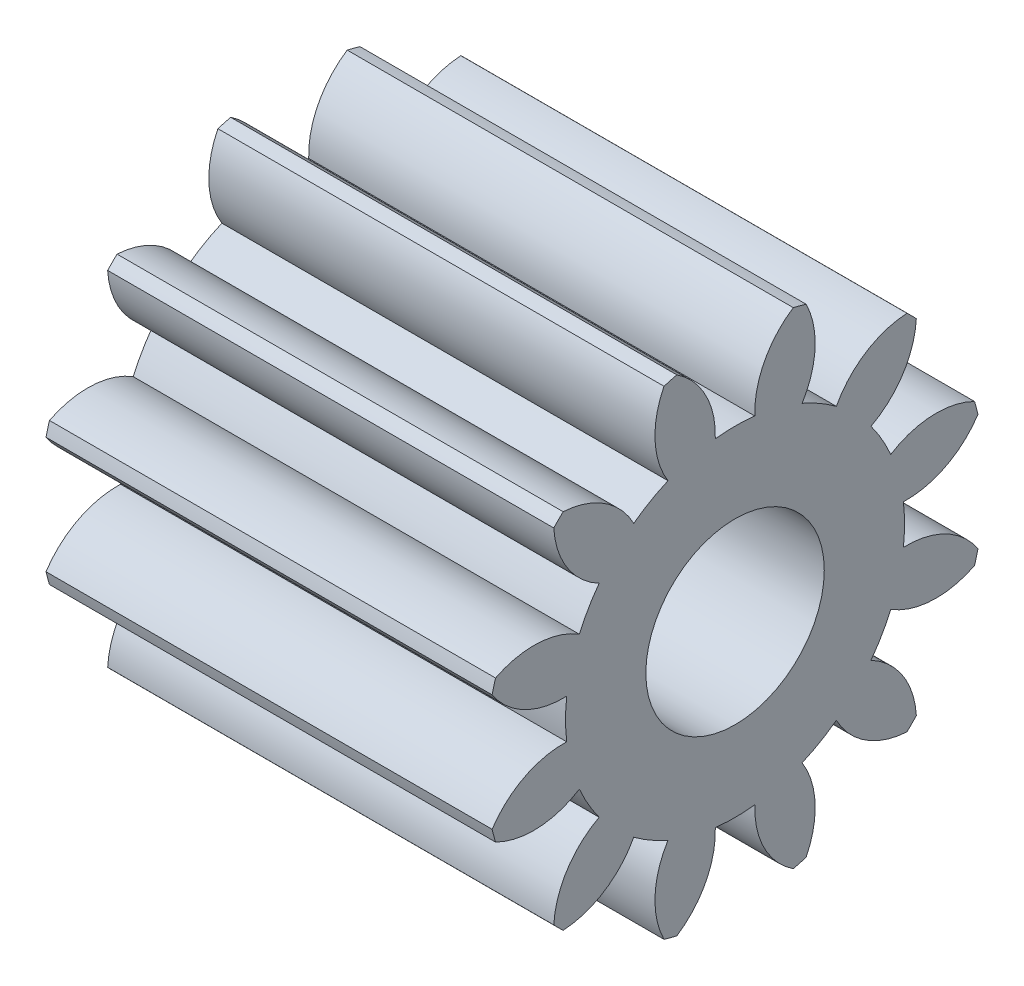
SolidWorks part; units mm, degrees
ref_plane "Plane1" through (0, 0, 0) normal (0, 0, 1) x (1, 0, 0)
ref_plane "Plane2" through (0, 0, 0) normal (0, 1, 0) x (1, 0, 0)
ref_plane "Plane3" through (0, 0, 0) normal (1, 0, 0) x (0, 0, -1)
sketch "HoldingSke" [suppressed] plane through (0, 0, 0) normal (0, 1, 0) x (1, 0, 0)
  line L0 (0, 0) -> (0.1223, -0.026)
  line L1 (-15, 0) -> (100, 0) construction
  line L2 (0, 0) -> (-2.1039, 2.3779)
  line L3 (0, 0) -> (-11.863, 4.5341)
  line L4 (0, 0) -> (8.4473, 1.7955)
  line L5 (0, 0) -> (-46.8476, -17.4728)
  line L6 (0, 0) -> (-82.8963, -55.9304)
  line L7 (-2.1039, 2.3779) -> (19.4211, 100.0338)
  line L8 (-76.2, 54.61) -> (-72.9, 54.61)
  line L9 (-71.009, 38.7566) -> (-53.1078, 45.2721)
  line L10 (-76.2, 71.12) -> (104.1128, 71.12)
  line L11 (0, 0) -> (-100, 0)
  line L12 (-76.2, 101.6) -> (-75.945, 101.6)
  line L13 (24.9733, 27.94) -> (52.9518, 28.4284)
  line L14 (24.9733, 27.94) -> (24.9743, 27.94)
  line L15 (24.9733, 27.94) -> (100.4006, 29.5858)
  line L16 (-63.627, -8) -> (-12.827, -8)
  circle A0 centre (0, 0) radius 20
  circle A1 centre (0, 0) radius 37.5
  circle A2 centre (0, 0) radius 37.5
  circle A3 centre (0, 0) radius 20
  dimension "MHD" = 75
  dimension "Hub_dia" = 75
  dimension "Bore" = 40
  dimension "MBD" = 40
  dimension "Num_teeth" = 12
  dimension "Pitch" = 0.125
  dimension "Overall_len" = 50
  dimension "Show_teeth" = 12
  dimension "Thickness" = 100
  dimension "OAL" = 100.0001
  dimension "T_dim" = 3.3
  dimension "Ap" = 20
  dimension "H" = 19.05
  dimension "Pitch_radius" = 180.3128
  dimension "Width" = 100
  dimension "Backlash" = 0.255
  dimension "Addendum_fac" = 1
  dimension "Dedendum_fac" = 1.25
  dimension "Clearance_fac" = 0.25
  dimension "Dedendum_add" = 0.001
  dimension "Module" = 8
sketch "BasProSke" plane through (0, 0, 0) normal (0, 1, 0) x (1, 0, 0)
  line L0 (-10, 0) -> (60, 0) construction
  line L1 (0, 0) -> (0, 56)
  line L2 (0, 0) -> (100, 0)
  line L3 (100, 0) -> (100, 56)
  line L4 (100, 56) -> (0, 56)
  dimension "Thickness" = 100
  dimension "Diameter" = 112
revolve "Base-Revolve" add sketch "BasProSke" angle 360 about L0
sketch "TooCutSke" plane through (0, 0, 0) normal (1, 0, 0) x (0, 0, -1)
  line L1 (0, 0) -> (0, 107) construction
  line L2 (0, 0) -> (-6.711, 47.5285) construction
  line L3 (0, 0) -> (-24.6634, 92.045) construction
  line L4 (-6.711, 47.5285) -> (-12.3317, 46.0225) construction
  arc A0 (4.4295, 37.7399) -> (-4.4295, 37.7399) centre (0, 0) ccw
  arc A1 (13.0788, 54.4774) -> (-13.0788, 54.4774) centre (0, 0) ccw
  circle A2 centre (0, 0) radius 48 construction
  circle A3 centre (0, 0) radius 45.1052 construction
  arc A4 (-4.4295, 37.7399) -> (-13.0788, 54.4774) centre (-23.6172, 38.428) ccw
  arc A5 (13.0788, 54.4774) -> (4.4295, 37.7399) centre (23.6172, 38.428) ccw
  dimension "Root_dia" = 75.998
  dimension "Overcut_dia" = 112.0508
  dimension "Pitch_dia" = 96
  dimension "Base_dia" = 90.2105
  dimension "Flank_rad" = 19.2
  dimension "Half_ang" = 15
  dimension "Half_CT" = 5.819
extrude "ToothCut" cut sketch "TooCutSke" along normal through all
fillet "Breaks" [suppressed] radius 0.16
fillet "RootFillets" [suppressed] radius 2.001
pattern_circular "TeethCuts" count 12 every 30 about axis through (-10, 0, 0) along (1, 0, 0) of "ToothCut", "RootFillets", "Breaks"
sketch "HubNeaOneSke" plane through (0, 0, 0) normal (-1, 0, 0) x (0, 0, 1)
  circle A0 centre (0, 0) radius 37.5
  dimension "Diameter" = 75
extrude "HubNearOne" [suppressed] add sketch "HubNeaOneSke" along normal blind 12.7001
sketch "HubNeaBotSke" plane through (0, 0, 0) normal (-1, 0, 0) x (0, 0, 1)
  circle A0 centre (0, 0) radius 37.5
  dimension "Diameter" = 75
extrude "HubNearBoth" [suppressed] add sketch "HubNeaBotSke" along normal blind 6.35
ref_plane "FarPln" through (100, 0, 0) normal (1, 0, 0) x (0, 0, -1)
sketch "HubFarSke" plane through (100, 0, 0) normal (1, 0, 0) x (0, 0, -1)
  circle A0 centre (0, 0) radius 37.5
  dimension "Diameter" = 75
extrude "HubFar" [suppressed] add sketch "HubFarSke" along normal blind 6.35
sketch "BorSke" plane through (0, 0, 0) normal (1, 0, 0) x (0, 0, -1)
  circle A0 centre (0, 0) radius 20
  dimension "Diameter" = 40
extrude "Bore" cut sketch "BorSke" along normal mid plane 200.0001
sketch "KeySke" plane through (0, 0, 0) normal (1, 0, 0) x (0, 0, -1)
  line L0 (-6, 0) -> (-6, 23.3)
  line L1 (-6, 23.3) -> (6, 23.3)
  line L2 (6, 23.3) -> (6, 0)
  line L3 (0, 0) -> (0, 34) construction
  line L4 (-6, 0) -> (6, 0)
  dimension "Offset" = 23.3
  dimension "Width" = 12
extrude "Keyway" [suppressed] cut sketch "KeySke" along normal mid plane 200.0001
pattern_circular "Keyway2" [suppressed] count 2 every 90 about axis through (-10, 0, 0) along (1, 0, 0)
scale "Scale1" scale about centroid uniform scaling yes scale factor 0.25
equation "' \"Module@HoldingSke\" = 6.35"
equation "' \"Num_teeth@HoldingSke\" = 12"
equation "' \"Ap@HoldingSke\" =  20"
equation "' \"Ap@HoldingSke\" = 20"
equation "' \"Width@HoldingSke\" = 0.5 * 25.4"
equation "' \"Hub_dia@HoldingSke\"= 1 * 25.4"
equation "' \"Hub_dia@HoldingSke\" = 1 * 25.4"
equation "' \"Overall_len@HoldingSke\" = 1.0 * 25.4"
equation "' \"Bore@HoldingSke\" = 0.75 * 25.4"
equation "' \"T_dim@HoldingSke\" = 0.1 * 25.4"
equation "' \"Width@KeySke\" = 0.25 * 25.4"
equation "' \"Show_teeth@HoldingSke\" = 13"
equation "' \"Backlash@HoldingSke\" = 0.009 * 25.4"
equation "' \"Addendum_fac@HoldingSke\" = 1.0"
equation "' \"Dedendum_fac@HoldingSke\" = 1.25"
equation "' \"Dedendum_add@HoldingSke\" = 0.00005 * 25.4"
equation "' \"Clearance_fac@HoldingSke\" = 0.25"
equation "\"Pitch@HoldingSke\" = 1 / \"Module@HoldingSke\""
equation "\"Overcut_dia@TooCutSke\" = (\"Num_teeth@HoldingSke\" + 2 * \"Addendum_fac@HoldingSke\") / \"Pitch@HoldingSke\" + 0.002 * 25.4"
equation "\"Pitch_dia@TooCutSke\" = \"Num_teeth@HoldingSke\" / \"Pitch@HoldingSke\""
equation "\"Base_dia@TooCutSke\" = \"Num_teeth@HoldingSke\" / \"Pitch@HoldingSke\" * cos((\"Ap@HoldingSke\"  * 3.14159265 / 180))"
equation "\"Root_dia@TooCutSke\" = (\"Num_teeth@HoldingSke\" + 2) / \"Pitch@HoldingSke\" - 2 * (\"Addendum_fac@HoldingSke\" + \"Dedendum_fac@HoldingSke\") / \"Pitch@HoldingSke\" - \"Dedendum_add@HoldingSke\" * 2"
equation "\"Half_ang@TooCutSke\" = 180 / \"Num_teeth@HoldingSke\""
equation "\"Half_CT@TooCutSke\" = \"Num_teeth@HoldingSke\" / \"Pitch@HoldingSke\" * sin((3.14159265 / 2 / \"Num_teeth@HoldingSke\")) / 2 - 7 * \"Backlash@HoldingSke\" / 4"
equation "\"Flank_rad@TooCutSke\" = \"Num_teeth@HoldingSke\" / \"Pitch@HoldingSke\" / 5"
equation "\"Radius@RootFillets\" = \"Clearance_fac@HoldingSke\" / \"Pitch@HoldingSke\" + \"Dedendum_add@HoldingSke\""
equation "\"Break_rad@Breaks\" = 0.02 / \"Pitch@HoldingSke\""
equation "\"Thickness@HoldingSke\" = \"Width@HoldingSke\""
equation "\"OAL@HoldingSke\" = \"Thickness@HoldingSke\""
equation "\"MHD@HoldingSke\" = (\"Num_teeth@HoldingSke\" + 2) / \"Pitch@HoldingSke\" - 2 * (\"Addendum_fac@HoldingSke\" + \"Dedendum_fac@HoldingSke\")  / \"Pitch@HoldingSke\" - \"Dedendum_add@HoldingSke\" * 2"
equation "\"MBD@HoldingSke\" = (\"Num_teeth@HoldingSke\" + 2) / \"Pitch@HoldingSke\" - 2 * (\"Addendum_fac@HoldingSke\" + \"Dedendum_fac@HoldingSke\")  / \"Pitch@HoldingSke\" - \"Dedendum_add@HoldingSke\" * 2 - 0.002 * 25.4"
equation "\"MHD@HoldingSke\" = ((sgn( \"MHD@HoldingSke\" - \"Hub_dia@HoldingSke\" )-1)*( \"MHD@HoldingSke\" - \"Hub_dia@HoldingSke\" ))/-2+ \"Hub_dia@HoldingSke\""
equation "\"MBD@HoldingSke\" = ((sgn( \"MBD@HoldingSke\" - \"Bore@HoldingSke\" )-1)*( \"MBD@HoldingSke\" - \"Bore@HoldingSke\" ))/-2+ \"Bore@HoldingSke\""
equation "\"OAL@HoldingSke\" = ((sgn( \"OAL@HoldingSke\" - \"Overall_len@HoldingSke\" )+1)*( \"OAL@HoldingSke\" - \"Overall_len@HoldingSke\" ))/2 + \"Overall_len@HoldingSke\" + 0.000002 * 25.4"
equation "\"Num_teeth@TeethCuts\" = int( \"Show_teeth@HoldingSke\" ) + 1"
equation "\"Num_teeth@TeethCuts\" = ((sgn( \"Num_teeth@TeethCuts\" - \"Num_teeth@HoldingSke\" )-1)*( \"Num_teeth@TeethCuts\" - \"Num_teeth@HoldingSke\" ))/-2+ \"Num_teeth@HoldingSke\""
equation "\"Num_teeth@TeethCuts\" = ((sgn( \"Num_teeth@TeethCuts\" - 2.0)+1)*( \"Num_teeth@TeethCuts\" - 2.0))/2 +2.0"
equation "\"Angle@TeethCuts\" = 360.0 / \"Num_teeth@HoldingSke\""
equation "\"Diameter@BasProSke\" = (\"Num_teeth@HoldingSke\" + 2 * \"Addendum_fac@HoldingSke\") / \"Pitch@HoldingSke\""
equation "\"Thickness@BasProSke\"  = \"Thickness@HoldingSke\""
equation "' \"Fillet_rad@BasProSke\" =  \"Thickness@HoldingSke\" * 0.05"
equation "' \"Fillet_rad@BasProSke\" = \"Thickness@HoldingSke\" * 0.05"
equation "\"MHD@HoldingSke\" = ((sgn( \"MHD@HoldingSke\" - \"Root_dia@TooCutSke\" )-1)*( \"MHD@HoldingSke\" - \"Root_dia@TooCutSke\" ))/-2+ \"Root_dia@TooCutSke\""
equation "\"Diameter@HubNeaOneSke\" = \"MHD@HoldingSke\""
equation "\"Length@HubNearOne\" = \"OAL@HoldingSke\" - \"Thickness@BasProSke\""
equation "\"Diameter@HubNeaBotSke\" = \"MHD@HoldingSke\""
equation "\"Length@HubNearBoth\" = ( \"OAL@HoldingSke\" - \"Thickness@BasProSke\" ) / 2.0"
equation "\"Thickness@FarPln\" = \"Thickness@BasProSke\""
equation "\"Diameter@HubFarSke\" = \"MHD@HoldingSke\""
equation "\"Length@HubFar\" = ( \"OAL@HoldingSke\" - \"Thickness@BasProSke\" ) / 2.0"
equation "\"Diameter@BorSke\" = \"MBD@HoldingSke\""
equation "\"D1@Bore\" = \"OAL@HoldingSke\" * 2.0"
equation "\"D1@Keyway\" = \"OAL@HoldingSke\" * 2.0"
equation "\"Offset@KeySke\" = \"T_dim@HoldingSke\" + \"MBD@HoldingSke\" / 2.0"
